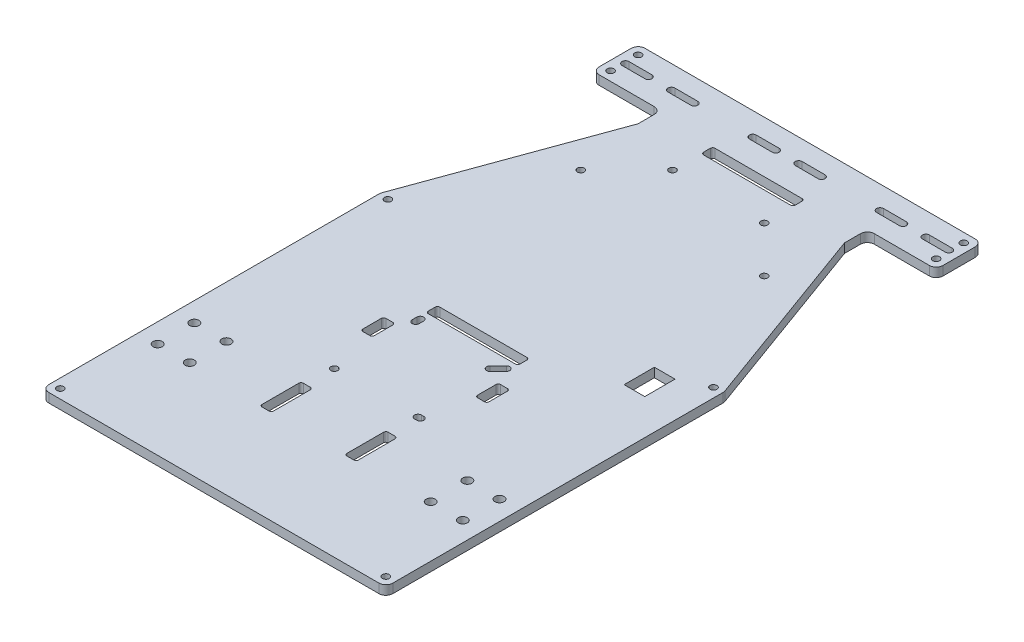
SolidWorks part; units mm, degrees
ref_plane "Front Plane" through (0, 0, 0) normal (0, 0, 1) x (1, 0, 0)
ref_plane "Top Plane" through (0, 0, 0) normal (0, 1, 0) x (1, 0, 0)
ref_plane "Right Plane" through (0, 0, 0) normal (1, 0, 0) x (0, 0, -1)
sketch "Sketch1" plane through (0, 0, 0) normal (0, 1, 0) x (1, 0, 0)
  line L0 (-72, 110) -> (-48, 110)
  line L1 (72, 130) -> (-72, 130)
  line L2 (75, 127) -> (75, 113)
  line L3 (72, -130) -> (-72, -130)
  line L4 (-75, 127) -> (-75, 113)
  line L5 (75, 130) -> (-75, -130) construction
  line L6 (75, -130) -> (-75, 130) construction
  line L7 (-45, 107) -> (-45, 100)
  line L8 (-45, 100) -> (-74.8191, 18.0728)
  line L9 (0, 0) -> (0, 130) construction
  line L10 (-75, 17.0467) -> (-75, -127)
  line L11 (45, 100) -> (74.8191, 18.0728)
  line L12 (45, 107) -> (45, 100)
  line L13 (72, 110) -> (48, 110)
  line L14 (75, 17.0467) -> (75, -127)
  line L15 (-75, 120) -> (75, 120) construction
  line L16 (-70.5, 121.5) -> (-60.5, 121.5)
  line L17 (-60.5, 118.5) -> (-70.5, 118.5)
  line L26 (-20, 90) -> (20, 90) construction
  line L27 (-75, -80) -> (75, -80) construction
  line L28 (0, 0) -> (0, -130) construction
  line L29 (-41.5, -93) -> (-72.5, -93) construction
  line L30 (-41.5, -93) -> (-41.5, -67) construction
  line L31 (-41.5, -67) -> (-72.5, -67) construction
  line L32 (-72.5, -93) -> (-72.5, -67) construction
  line L33 (-41.5, -93) -> (-72.5, -67) construction
  line L34 (-41.5, -67) -> (-72.5, -93) construction
  line L35 (-21.5, -40) -> (21.5, -40) construction
  line L36 (-21.5, -18.5) -> (21.5, -18.5) construction
  line L37 (-21.5, -18.5) -> (-21.5, -61.5) construction
  line L38 (-21.5, -61.5) -> (21.5, -61.5) construction
  line L39 (21.5, -18.5) -> (21.5, -61.5) construction
  line L40 (-21.5, -18.5) -> (21.5, -61.5) construction
  line L41 (-21.5, -61.5) -> (21.5, -18.5) construction
  line L43 (-19, -12.5) -> (19, -12.5)
  line L44 (-20, -13.5) -> (-20, -16.5)
  line L45 (-19, -17.5) -> (19, -17.5)
  line L46 (20, -13.5) -> (20, -16.5)
  line L47 (-20, -12.5) -> (20, -17.5) construction
  line L48 (-20, -17.5) -> (20, -12.5) construction
  line L52 (-15, 121.5) -> (-5, 121.5)
  line L53 (59.5, 11.6) -> (50.5, 11.6)
  line L54 (59.5, 11.6) -> (59.5, -1.6)
  line L55 (59.5, -1.6) -> (50.5, -1.6)
  line L56 (50.5, 11.6) -> (50.5, -1.6)
  line L57 (59.5, 11.6) -> (50.5, -1.6) construction
  line L58 (59.5, -1.6) -> (50.5, 11.6) construction
  line L59 (-50.5, 121.5) -> (-40.5, 121.5)
  line L60 (-40.5, 118.5) -> (-50.5, 118.5)
  line L61 (-5, 118.5) -> (-15, 118.5)
  line L62 (5, 118.5) -> (15, 118.5)
  line L63 (15, 121.5) -> (5, 121.5)
  line L64 (-20, 79.5) -> (20, 79.5) construction
  line L65 (19, 102.5) -> (-19, 102.5)
  line L66 (20, 103.5) -> (20, 106.5)
  line L67 (19, 107.5) -> (-19, 107.5)
  line L68 (-20, 103.5) -> (-20, 106.5)
  line L69 (20, 102.5) -> (-20, 107.5) construction
  line L70 (20, 107.5) -> (-20, 102.5) construction
  line L82 (-18.75, -21.25) -> (-18.75, -23.25) construction
  line L83 (-17.25, -21.25) -> (-17.25, -23.25)
  line L84 (-20.25, -21.25) -> (-20.25, -23.25)
  line L85 (18.75, -58.75) -> (17.75, -58.75) construction
  line L86 (18.75, -60.25) -> (17.75, -60.25)
  line L87 (18.75, -57.25) -> (17.75, -57.25)
  line L88 (18.75, -21.25) -> (15.2145, -24.7855) construction
  line L89 (19.8107, -22.3107) -> (16.2751, -25.8462)
  line L90 (17.6893, -20.1893) -> (14.1538, -23.7249)
  line L91 (50.5, 121.5) -> (40.5, 121.5)
  line L92 (40.5, 118.5) -> (50.5, 118.5)
  line L93 (60.5, 118.5) -> (70.5, 118.5)
  line L94 (70.5, 121.5) -> (60.5, 121.5)
  arc A0 (-72, -130) -> (-75, -127) centre (-72, -127) cw
  arc A1 (75, -127) -> (72, -130) centre (72, -127) cw
  arc A2 (74.8191, 18.0728) -> (75, 17.0467) centre (72, 17.0467) cw
  arc A3 (-74.8191, 18.0728) -> (-75, 17.0467) centre (-72, 17.0467) ccw
  arc A4 (-48, 110) -> (-45, 107) centre (-48, 107) cw
  arc A5 (45, 107) -> (48, 110) centre (48, 107) cw
  arc A6 (72, 130) -> (75, 127) centre (72, 127) cw
  arc A7 (72, 110) -> (75, 113) centre (72, 113) ccw
  arc A8 (-72, 130) -> (-75, 127) centre (-72, 127) ccw
  arc A9 (-72, 110) -> (-75, 113) centre (-72, 113) cw
  arc A10 (-70.5, 121.5) -> (-70.5, 118.5) centre (-70.5, 120) ccw
  arc A11 (-60.5, 118.5) -> (-60.5, 121.5) centre (-60.5, 120) ccw
  circle A20 centre (20, 90) radius 1.5
  circle A21 centre (-20, 90) radius 1.5
  circle A22 centre (-66.5385, -72) radius 2
  circle A23 centre (-66.5385, -88) radius 2
  circle A24 centre (-52.5385, -72) radius 2
  circle A25 centre (-52.5385, -88) radius 2
  circle A26 centre (52.5385, -88) radius 2
  circle A27 centre (66.5385, -88) radius 2
  circle A28 centre (66.5385, -72) radius 2
  circle A29 centre (52.5385, -72) radius 2
  circle A31 centre (-18.75, -58.75) radius 1.5
  arc A34 (-40.5, 118.5) -> (-40.5, 121.5) centre (-40.5, 120) ccw
  arc A35 (-50.5, 121.5) -> (-50.5, 118.5) centre (-50.5, 120) ccw
  arc A36 (-5, 118.5) -> (-5, 121.5) centre (-5, 120) ccw
  arc A37 (5, 121.5) -> (5, 118.5) centre (5, 120) ccw
  arc A38 (-15, 121.5) -> (-15, 118.5) centre (-15, 120) ccw
  arc A39 (15, 121.5) -> (15, 118.5) centre (15, 120) cw
  arc A40 (-19, 107.5) -> (-20, 106.5) centre (-19, 106.5) ccw
  arc A41 (-19, 102.5) -> (-20, 103.5) centre (-19, 103.5) cw
  arc A42 (19, 102.5) -> (20, 103.5) centre (19, 103.5) ccw
  arc A43 (20, 106.5) -> (19, 107.5) centre (19, 106.5) ccw
  arc A47 (-20, -16.5) -> (-19, -17.5) centre (-19, -16.5) ccw
  arc A48 (-19, -12.5) -> (-20, -13.5) centre (-19, -13.5) ccw
  arc A49 (19, -17.5) -> (20, -16.5) centre (19, -16.5) ccw
  arc A50 (19, -12.5) -> (20, -13.5) centre (19, -13.5) cw
  arc A63 (-17.25, -21.25) -> (-20.25, -21.25) centre (-18.75, -21.25) ccw
  arc A64 (-20.25, -23.25) -> (-17.25, -23.25) centre (-18.75, -23.25) ccw
  arc A65 (18.75, -60.25) -> (18.75, -57.25) centre (18.75, -58.75) ccw
  arc A66 (17.75, -57.25) -> (17.75, -60.25) centre (17.75, -58.75) ccw
  arc A67 (19.8107, -22.3107) -> (17.6893, -20.1893) centre (18.75, -21.25) ccw
  arc A68 (14.1538, -23.7249) -> (16.2751, -25.8462) centre (15.2145, -24.7855) ccw
  arc A69 (40.5, 118.5) -> (40.5, 121.5) centre (40.5, 120) cw
  arc A70 (50.5, 121.5) -> (50.5, 118.5) centre (50.5, 120) cw
  arc A71 (70.5, 121.5) -> (70.5, 118.5) centre (70.5, 120) cw
  arc A72 (60.5, 118.5) -> (60.5, 121.5) centre (60.5, 120) cw
  point P0 (0, 0)
  point P24 (75, 17.5757)
  point P27 (-75, 17.5757)
  point P30 (-45, 110)
  point P33 (45, 110)
  point P39 (75, 110)
  point P45 (-75, 110)
  point P65 (0, 105)
  point P81 (0, 90)
  point P85 (-57, -80)
  point P107 (0, -40)
  point P122 (0, -15)
  point P131 (55, 5)
  point P172 (0, 79.5)
  point P237 (-18.75, -22.25)
  point P243 (18.25, -58.75)
  point P249 (16.9822, -23.0178)
  dimension "D7" = 3
  dimension "D8" = 3
  dimension "D9" = 3
  dimension "D14" = 3
  dimension "D15" = 3
  dimension "D20" = 4
  dimension "D21" = 4
  dimension "D23" = 4
  dimension "D24" = 4
  dimension "D30" = 2
  dimension "D31" = 3
  dimension "D41" = 5
  dimension "D42" = 3
  dimension "D44" = 3
  dimension "D48" = 1
  dimension "D56" = 1
  dimension "D62" = 1.5
  dimension "D63" = 1.5
  dimension "D64" = 1.5
  dimension "D1" = 150
  dimension "D2" = 260
  dimension "D3" = 20
  dimension "D4" = 10
  dimension "D5" = 160
  dimension "D6" = 30
  dimension "D10" = 10
  dimension "D11" = 4.5
  dimension "D13" = 40
  dimension "D12" = 40
  dimension "D16" = 50
  dimension "D17" = 31
  dimension "D18" = 26
  dimension "D19" = 18
  dimension "D22" = 16
  dimension "D25" = 14
  dimension "D26" = 16
  dimension "D27" = 43
  dimension "D28" = 43
  dimension "D29" = 90
  dimension "D32" = 37.5
  dimension "D33" = 5
  dimension "D34" = 40
  dimension "D35" = 115
  dimension "D36" = 13.2
  dimension "D37" = 9
  dimension "D38" = 135
  dimension "D39" = 20
  dimension "D40" = 5
  dimension "D43" = 10
  dimension "D45" = 10
  dimension "D46" = 40
  dimension "D47" = 25
  dimension "D49" = 40
  dimension "D50" = 23
  dimension "D65" = 1
  dimension "D66" = 2
extrude "Boss-Extrude1" add sketch "Sketch1" along normal blind 4
sketch "Sketch2" plane through (0, 4, 0) normal (0, 1, 0) x (1, 0, 0)
  line L1 (21, -89) -> (16, -71) construction
  line L5 (-20, -71) -> (-17, -71)
  line L6 (0, -130) -> (0, 130) construction
  line L7 (-72, -130) -> (72, -130) construction
  line L8 (72, 130) -> (-72, 130) construction
  line L13 (-21.5, -18.5) -> (21.5, -18.5) construction
  line L14 (-26.5, -28.5) -> (-23.5, -28.5)
  line L15 (-27.5, -29.5) -> (-27.5, -37.5)
  line L16 (-26.5, -38.5) -> (-23.5, -38.5)
  line L17 (-22.5, -29.5) -> (-22.5, -37.5)
  line L18 (-27.5, -28.5) -> (-22.5, -38.5) construction
  line L19 (-27.5, -38.5) -> (-22.5, -28.5) construction
  line L20 (27.5, -38.5) -> (22.5, -28.5) construction
  line L21 (27.5, -28.5) -> (22.5, -38.5) construction
  line L22 (26.5, -38.5) -> (23.5, -38.5)
  line L23 (27.5, -29.5) -> (27.5, -37.5)
  line L24 (26.5, -28.5) -> (23.5, -28.5)
  line L25 (22.5, -29.5) -> (22.5, -37.5)
  line L31 (-21, -72) -> (-21, -88)
  line L32 (-20, -89) -> (-17, -89)
  line L33 (-16, -72) -> (-16, -88)
  line L34 (-72, 110) -> (-48, 110) construction
  line L35 (-45, 100) -> (-74.8191, 18.0728) construction
  line L36 (-75, 17.0467) -> (-75, -127) construction
  line L37 (-21, -71) -> (-16, -89) construction
  line L38 (-21, -89) -> (-16, -71) construction
  line L39 (21, -71) -> (16, -89) construction
  line L40 (16, -72) -> (16, -88)
  line L41 (20, -89) -> (17, -89)
  line L42 (21, -72) -> (21, -88)
  line L43 (20, -71) -> (17, -71)
  arc A0 (-26.5, -28.5) -> (-27.5, -29.5) centre (-26.5, -29.5) ccw
  arc A1 (-27.5, -37.5) -> (-26.5, -38.5) centre (-26.5, -37.5) ccw
  arc A2 (-23.5, -38.5) -> (-22.5, -37.5) centre (-23.5, -37.5) ccw
  arc A3 (-23.5, -28.5) -> (-22.5, -29.5) centre (-23.5, -29.5) cw
  arc A4 (23.5, -28.5) -> (22.5, -29.5) centre (23.5, -29.5) ccw
  arc A5 (23.5, -38.5) -> (22.5, -37.5) centre (23.5, -37.5) cw
  arc A6 (27.5, -37.5) -> (26.5, -38.5) centre (26.5, -37.5) cw
  arc A7 (26.5, -28.5) -> (27.5, -29.5) centre (26.5, -29.5) cw
  circle A16 centre (-71, -126) radius 1.5
  circle A17 centre (-71, 16.8704) radius 1.5
  circle A18 centre (-71, 114) radius 1.5
  circle A19 centre (-71, 126) radius 1.5
  circle A20 centre (71, 16.8704) radius 1.5
  circle A21 centre (71, -126) radius 1.5
  circle A22 centre (71, 114) radius 1.5
  circle A23 centre (71, 126) radius 1.5
  circle A24 centre (-40, 70) radius 1.5
  circle A25 centre (40, 70) radius 1.5
  arc A26 (-20, -71) -> (-21, -72) centre (-20, -72) ccw
  arc A27 (-21, -88) -> (-20, -89) centre (-20, -88) ccw
  arc A28 (-17, -89) -> (-16, -88) centre (-17, -88) ccw
  arc A29 (-17, -71) -> (-16, -72) centre (-17, -72) cw
  arc A30 (17, -71) -> (16, -72) centre (17, -72) ccw
  arc A31 (17, -89) -> (16, -88) centre (17, -88) cw
  arc A32 (21, -88) -> (20, -89) centre (20, -88) cw
  arc A33 (20, -71) -> (21, -72) centre (20, -72) cw
  point P0 (-18.5, -80)
  point P18 (-25, -33.5)
  point P53 (25, -33.5)
  point P76 (18.5, -80)
  dimension "D8" = 1
  dimension "D9" = 50
  dimension "D13" = 1
  dimension "D19" = 3
  dimension "D20" = 3
  dimension "D26" = 3
  dimension "D27" = 3
  dimension "D30" = 3
  dimension "D4" = 5
  dimension "D5" = 10
  dimension "D6" = 25
  dimension "D7" = 15
  dimension "D10" = 56.5
  dimension "D11" = 5
  dimension "D12" = 18
  dimension "D21" = 4
  dimension "D22" = 4
  dimension "D23" = 4
  dimension "D24" = 4
  dimension "D25" = 4
  dimension "D28" = 4
  dimension "D29" = 4
  dimension "D31" = 40
  dimension "D32" = 60
extrude "Cut-Extrude1" cut sketch "Sketch2" against normal blind 4
